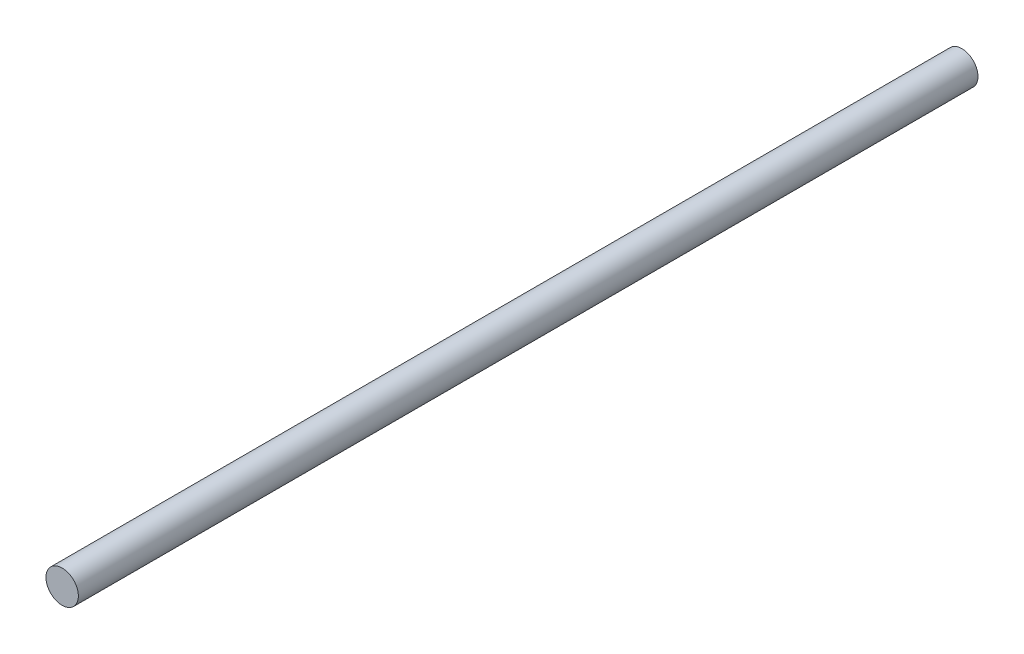
SolidWorks part; units mm, degrees
ref_plane "Front Plane" through (0, 0, 0) normal (0, 0, 1) x (1, 0, 0)
ref_plane "Top Plane" through (0, 0, 0) normal (0, 1, 0) x (1, 0, 0)
ref_plane "Right Plane" through (0, 0, 0) normal (1, 0, 0) x (0, 0, -1)
sketch "Sketch1" plane through (0, 0, 0) normal (0, 0, 1) x (1, 0, 0)
  circle A0 centre (0, 0) radius 9
  dimension "D1" = 18
extrude "Boss-Extrude1" add sketch "Sketch1" along normal blind 500
